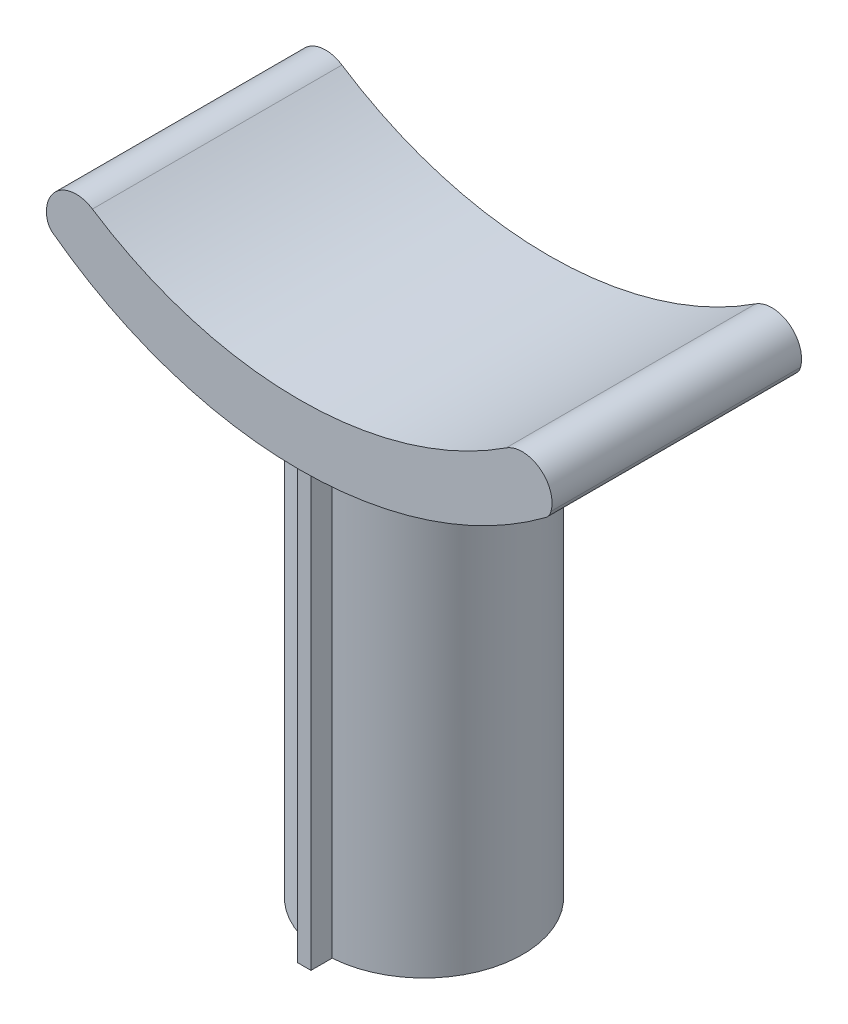
SolidWorks part; units mm, degrees
ref_plane "Front Plane" through (0, 0, 0) normal (0, 0, 1) x (1, 0, 0)
ref_plane "Top Plane" through (0, 0, 0) normal (0, 1, 0) x (1, 0, 0)
ref_plane "Right Plane" through (0, 0, 0) normal (1, 0, 0) x (0, 0, -1)
sketch "Sketch2" plane through (0, 0, 0) normal (0, 1, 0) x (1, 0, 0)
  circle A0 centre (0, 0) radius 12.15
  circle A1 centre (0, 0) radius 13.3
  dimension "D1" = 24.3
  dimension "D2" = 26.6
sketch "Sketch4" plane through (0, 0, 0) normal (0, 1, 0) x (1, 0, 0)
  line L1 (-0.9, -16.1203) -> (0.9, -16.1203)
  line L2 (0.9, -16.1203) -> (0.9, -13.1203)
  line L3 (0, 11.8855) -> (0, -21.5327) construction
  line L4 (0.9, -13.1203) -> (-0.9, -13.1203)
  line L5 (-0.9, -16.1203) -> (-0.9, -13.1203)
  dimension "D1" = 1.8
  dimension "D2" = 3
  dimension "D3" = 13.1203
sketch "Sketch6" plane through (0, 0, 0) normal (0, 0, 1) x (1, 0, 0)
  arc A0 (-27.85, 74.75) -> (27.85, 74.75) centre (0, 117.3242) ccw
  arc A1 (27.85, 74.75) -> (33.6255, 69.63) centre (30.0397, 71.4026) cw
  arc A4 (-27.85, 74.75) -> (-33.6255, 69.63) centre (-30.0397, 71.4026) ccw
  arc A5 (-33.6255, 69.63) -> (33.6255, 69.63) centre (0, 113.8624) ccw
  point P3 (0, 66.45)
  point P11 (0, 58.3)
  dimension "D4" = 8.3
  dimension "D3" = 5.12
  dimension "D5" = 4
  dimension "D6" = 58.3
  dimension "D1" = 55.7
  dimension "D2" = 66.45
extrude "Boss-Extrude1" add sketch "Sketch6" along normal mid plane 33.6
shell "Shell5" thickness 1.6
extrude "Boss-Extrude2" add sketch "Sketch2" along normal blind 66.45
extrude "Boss-Extrude3" add sketch "Sketch4" along normal blind 66.45
fillet "Fillet1" radius 2 4 edges at (33.6255, 69.63, -16) (33.6255, 69.63, 16) (-33.6255, 69.63, -16) (-33.6255, 69.63, 16)
sketch "Sketch7" plane through (0, 0, 0) normal (0, 0, 1) x (1, 0, 0)
  line L0 (-28.7259, 73.411) -> (-27.85, 74.75)
  line L1 (-32.2115, 70.5685) -> (-33.1666, 69.2849)
  line L2 (33.1666, 69.2849) -> (32.2115, 70.5685)
  line L3 (28.7259, 73.411) -> (27.85, 74.75)
  arc A0 (-33.9058, 70.3763) -> (-33.1666, 69.2849) centre (-31.9728, 70.8895) ccw construction
  arc A1 (33.1666, 69.2849) -> (33.9058, 70.3763) centre (31.9728, 70.8895) ccw construction
  arc A2 (33.9058, 70.3763) -> (27.85, 74.75) centre (30.0397, 71.4026) ccw construction
  arc A3 (-27.85, 74.75) -> (-33.9058, 70.3763) centre (-30.0397, 71.4026) ccw construction
  arc A4 (-33.9058, 70.3763) -> (-33.1666, 69.2849) centre (-31.9728, 70.8895) ccw
  arc A5 (33.1666, 69.2849) -> (33.9058, 70.3763) centre (31.9728, 70.8895) ccw
  arc A6 (33.9058, 70.3763) -> (27.85, 74.75) centre (30.0397, 71.4026) ccw
  arc A7 (-27.85, 74.75) -> (-33.9058, 70.3763) centre (-30.0397, 71.4026) ccw
  arc A8 (-28.7259, 73.411) -> (-32.3594, 70.7868) centre (-30.0397, 71.4026) ccw
  arc A9 (-32.3594, 70.7868) -> (-32.2115, 70.5685) centre (-31.9728, 70.8895) ccw
  arc A10 (32.2115, 70.5685) -> (32.3594, 70.7868) centre (31.9728, 70.8895) ccw
  arc A11 (32.3594, 70.7868) -> (28.7259, 73.411) centre (30.0397, 71.4026) ccw
  dimension "D1" = 1.6
extrude "Boss-Extrude4" add sketch "Sketch7" along normal mid plane 33.6
